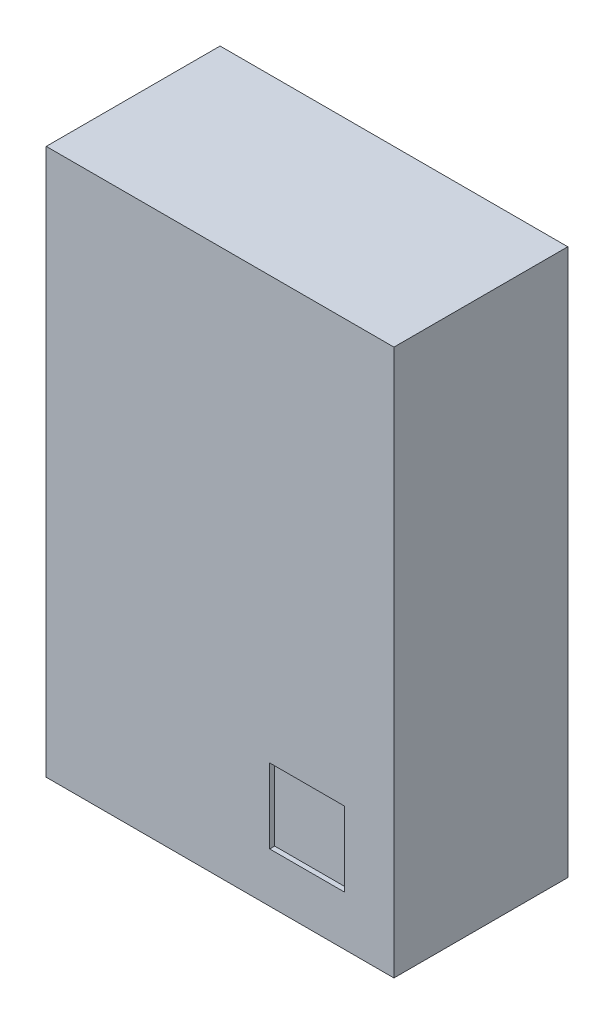
SolidWorks part; units mm, degrees
ref_plane "Front Plane" through (0, 0, 0) normal (0, 0, 1) x (1, 0, 0)
ref_plane "Top Plane" through (0, 0, 0) normal (0, 1, 0) x (1, 0, 0)
ref_plane "Right Plane" through (0, 0, 0) normal (1, 0, 0) x (0, 0, -1)
sketch "Sketch1" plane through (0, 0, 0) normal (0, 0, 1) x (1, 0, 0)
  line L1 (-0.35, 0.55) -> (0.35, 0.55)
  line L2 (-0.35, 0.55) -> (-0.35, -0.55)
  line L3 (-0.35, -0.55) -> (0.35, -0.55)
  line L4 (0.35, 0.55) -> (0.35, -0.55)
  line L5 (-0.35, 0.55) -> (0.35, -0.55) construction
  line L6 (-0.35, -0.55) -> (0.35, 0.55) construction
  point P0 (0, 0)
  dimension "D1" = 0.7
  dimension "D2" = 1.1
extrude "Boss-Extrude1" add sketch "Sketch1" along normal blind 0.35
sketch "Sketch2" plane through (0, 0, 0) normal (0, 0, -1) x (-1, 0, 0)
  line L0 (0, 0) -> (0, 0.55) construction
  line L1 (-0.3, 0.5) -> (-0.1, 0.5)
  line L2 (-0.3, 0.5) -> (-0.3, 0.3)
  line L3 (-0.3, 0.3) -> (-0.1, 0.3)
  line L4 (-0.1, 0.5) -> (-0.1, 0.3)
  line L5 (-0.3, 0.5) -> (-0.1, 0.3) construction
  line L6 (-0.3, 0.3) -> (-0.1, 0.5) construction
  line L7 (-0.35, 0.55) -> (0.35, 0.55) construction
  line L8 (0, 0) -> (-0.35, 0) construction
  line L9 (-0.35, -0.55) -> (-0.35, 0.55) construction
  line L10 (-0.3, -0.3) -> (-0.1, -0.3)
  line L11 (-0.3, 0.1) -> (-0.1, 0.1)
  line L12 (-0.3, 0.1) -> (-0.3, -0.1)
  line L13 (-0.3, -0.1) -> (-0.1, -0.1)
  line L14 (-0.1, 0.1) -> (-0.1, -0.1)
  line L15 (-0.3, 0.1) -> (-0.1, -0.1) construction
  line L16 (-0.3, -0.1) -> (-0.1, 0.1) construction
  line L17 (-0.1, -0.5) -> (-0.1, -0.3)
  line L18 (-0.3, -0.5) -> (-0.1, -0.5)
  line L19 (-0.3, -0.5) -> (-0.3, -0.3)
  line L20 (0.3, -0.5) -> (0.3, -0.3)
  line L21 (0.3, -0.5) -> (0.1, -0.5)
  line L22 (0.1, -0.5) -> (0.1, -0.3)
  line L23 (0.3, -0.3) -> (0.1, -0.3)
  line L24 (0.3, -0.1) -> (0.1, -0.1)
  line L25 (0.1, 0.1) -> (0.1, -0.1)
  line L26 (0.3, 0.1) -> (0.1, 0.1)
  line L27 (0.3, 0.1) -> (0.3, -0.1)
  line L28 (0.3, 0.3) -> (0.1, 0.3)
  line L29 (0.1, 0.5) -> (0.1, 0.3)
  line L30 (0.3, 0.5) -> (0.1, 0.5)
  line L31 (0.3, 0.5) -> (0.3, 0.3)
  point P0 (-0.2, 0.4)
  point P10 (-0.2, 0)
  dimension "D1" = 0.2
  dimension "D2" = 0.4
  dimension "D3" = 0.4
extrude "Boss-Extrude2" add sketch "Sketch2" along normal blind 0.02
sketch "Sketch3" plane through (0, 0, 0.35) normal (0, 0, 1) x (1, 0, 0)
  line L0 (0.35, -0.55) -> (0.35, 0.55) construction
  line L1 (0.25, -0.45) -> (0.1, -0.45)
  line L2 (0.25, -0.45) -> (0.25, -0.3)
  line L3 (0.25, -0.3) -> (0.1, -0.3)
  line L4 (0.1, -0.45) -> (0.1, -0.3)
  line L5 (-0.35, -0.55) -> (0.35, -0.55) construction
  dimension "D1" = 0.1
  dimension "D2" = 0.1
  dimension "D3" = 0.15
extrude "Cut-Extrude1" cut sketch "Sketch3" against normal blind 0.01
